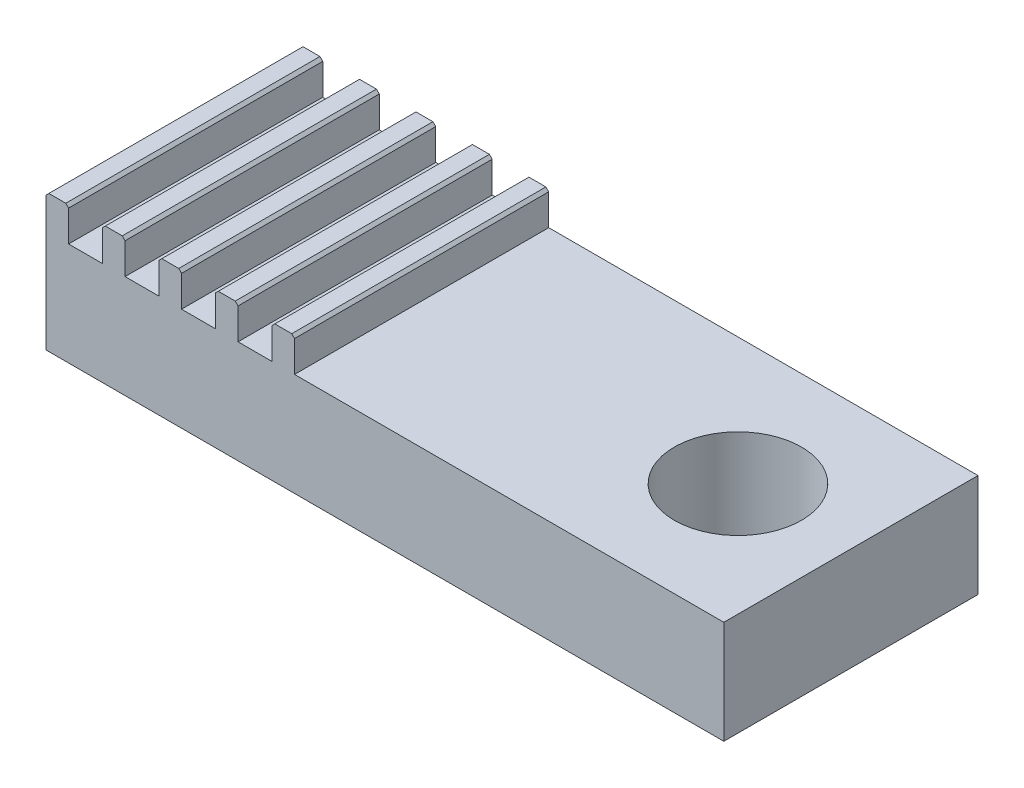
SolidWorks part; units mm, degrees
material "6063-T1"
ref_plane "Ön Düzlem" through (0, 0, 0) normal (0, 0, 1) x (1, 0, 0)
ref_plane "Üst Düzlem" through (0, 0, 0) normal (0, 1, 0) x (1, 0, 0)
ref_plane "Sağ Düzlem" through (0, 0, 0) normal (1, 0, 0) x (0, 0, -1)
sketch "Sketch1" plane through (0, 0, 0) normal (0, 0, 1) x (1, 0, 0)
  line L0 (28, 3.65) -> (28, 0)
  line L8 (4, 3.65) -> (4, 4.85)
  line L9 (4, 4.85) -> (4.8, 4.85)
  line L10 (4.8, 4.85) -> (4.8, 3.65)
  line L11 (4.8, 3.65) -> (6, 3.65)
  line L12 (6, 3.65) -> (6, 4.85)
  line L13 (6, 4.85) -> (6.8, 4.85)
  line L14 (6.8, 4.85) -> (6.8, 3.65)
  line L15 (6.8, 3.65) -> (8, 3.65)
  line L16 (8, 3.65) -> (8, 4.85)
  line L17 (8, 4.85) -> (8.8, 4.85)
  line L18 (8.8, 4.85) -> (8.8, 3.65)
  line L19 (8.8, 3.65) -> (10, 3.65)
  line L20 (10, 3.65) -> (10, 4.85)
  line L21 (10, 4.85) -> (10.8, 4.85)
  line L22 (10.8, 4.85) -> (10.8, 3.65)
  line L23 (10.8, 3.65) -> (12, 3.65)
  line L24 (12, 3.65) -> (12, 4.85)
  line L25 (12, 4.85) -> (12.8, 4.85)
  line L26 (12.8, 4.85) -> (12.8, 3.65)
  line L27 (12.8, 3.65) -> (28, 3.65)
  line L28 (4, 0) -> (28, 0)
  line L29 (20.4, -242.3971) -> (20.4, 11877.4577) construction
  line L57 (4, 3.65) -> (4, 0)
  point P34 (20.4, 0)
  point P35 (20.4, 3.65)
  dimension "D2" = 24
  dimension "D4" = 0.8
  dimension "D5" = 0.8
  dimension "D6" = 0.8
  dimension "D7" = 0.8
  dimension "D8" = 0.8
  dimension "D11" = 1.2
  dimension "D12" = 1.2
  dimension "D13" = 1.2
  dimension "D14" = 1.2
extrude "Boss-Extrude1" add sketch "Sketch1" along normal blind 9
chamfer "Chamfer1" distance 0.1 angle 45 10 edges at (12.8, 4.85, 4.5) (12, 4.85, 4.5) (10.8, 4.85, 4.5) (10, 4.85, 4.5) (8.8, 4.85, 4.5) (8, 4.85, 4.5) (6.8, 4.85, 4.5) (6, 4.85, 4.5) (4.8, 4.85, 4.5) (4, 4.85, 4.5)
sketch "Sketch2" plane through (0, 3.65, 0) normal (0, 1, 0) x (1, 0, 0)
  line L0 (4, -9) -> (4, 0) construction
  circle A0 centre (24, -4.5) radius 2.25
  dimension "D1" = 20
extrude "Cut-Extrude1" cut sketch "Sketch2" against normal through all
